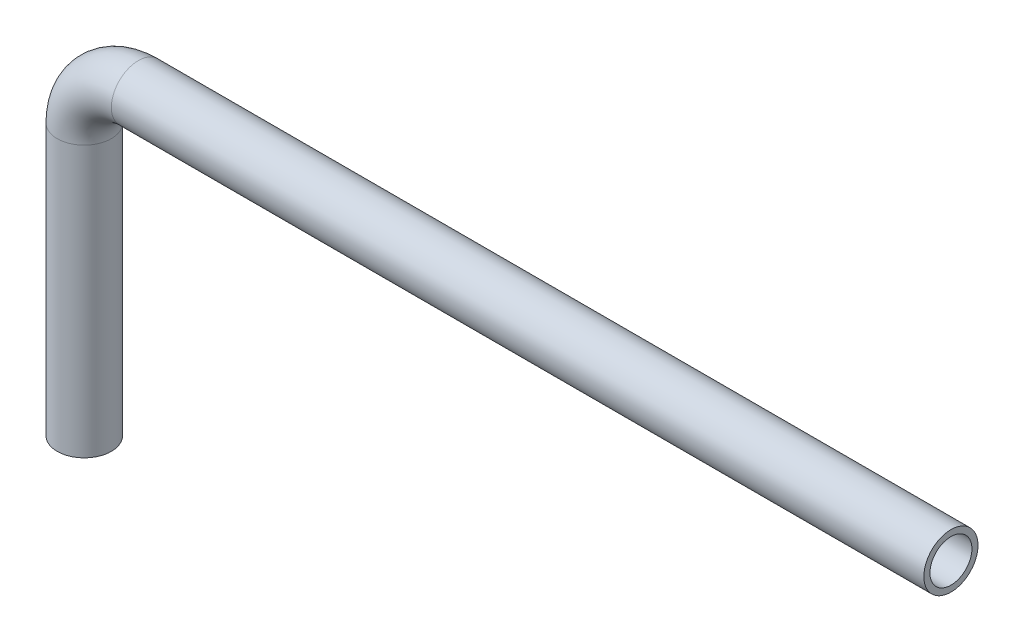
SolidWorks part; units mm, degrees
material "3003 Alloy"
ref_plane "Front Plane" through (0, 0, 0) normal (0, 0, 1) x (1, 0, 0)
ref_plane "Top Plane" through (0, 0, 0) normal (0, 1, 0) x (1, 0, 0)
ref_plane "Right Plane" through (0, 0, 0) normal (1, 0, 0) x (0, 0, -1)
sketch "Sketch1" plane through (0, 0, 0) normal (0, 1, 0) x (1, 0, 0)
  circle A0 centre (0, 0) radius 1.5875
  circle A1 centre (0, 0) radius 1.2319
  dimension "D1" = 3.175
  dimension "D2" = 2.4638
sketch "Sketch2" plane through (0, 0, 0) normal (0, 0, 1) x (1, 0, 0)
  line L0 (0, 0) -> (0, 15.875)
  line L1 (1.5875, 0) -> (-1.5875, 0) construction
  line L2 (3.175, 19.05) -> (50.8, 19.05)
  arc A0 (0, 15.875) -> (3.175, 19.05) centre (3.175, 15.875) cw
  point P7 (0, 19.05)
  dimension "D3" = 3.175
  dimension "D1" = 19.05
  dimension "D2" = 50.8
sweep "Sweep1" add profiles "Sketch1" path "Sketch2"
